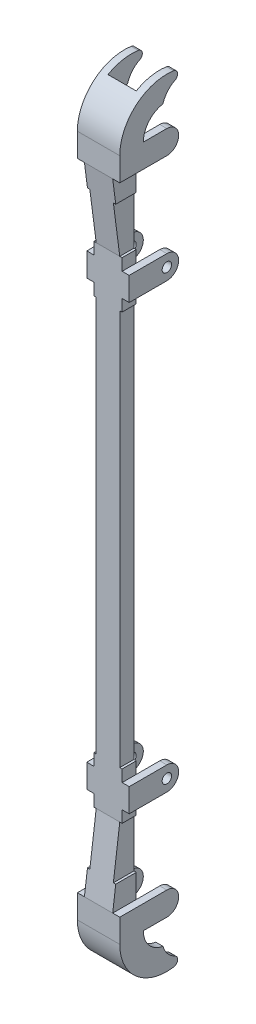
SolidWorks part; units mm, degrees
ref_plane "Ebene vorne" through (0, 0, 0) normal (0, 0, 1) x (1, 0, 0)
ref_plane "Ebene oben" through (0, 0, 0) normal (0, 1, 0) x (1, 0, 0)
ref_plane "Ebene rechts" through (0, 0, 0) normal (1, 0, 0) x (0, 0, -1)
sketch "Skizze2" plane through (0, 0, -2.5) normal (0, 0, 1) x (1, 0, 0)
  line L0 (2.5, -19.8333) -> (-2.5, -19.8333) construction
  line L1 (-2.5, -92.3333) -> (2.5, -92.3333)
  line L2 (-2.5, -92.3333) -> (-2.5, 52.6667)
  line L3 (-2.5, 52.6667) -> (2.5, 52.6667)
  line L4 (2.5, -92.3333) -> (2.5, 52.6667)
  line L5 (-2.5, -92.3333) -> (2.5, 52.6667) construction
  line L6 (-2.5, 52.6667) -> (2.5, -92.3333) construction
  line L7 (2.5, -3.25) -> (2.5, -36.4167) construction
  line L8 (2.5, 36.4167) -> (2.5, 3.25) construction
  line L9 (-2.5, 62.6667) -> (2.5, 62.6667) construction
  point P0 (0, -19.8333)
  dimension "D1" = 10
extrude "Aufsatz-Linear austragen1" add sketch "Skizze2" along normal blind 3 from surface at 2.5
sketch "Skizze3" plane through (2.5, 0, 0) normal (1, 0, 0) x (0, 0, -1)
  line L0 (0, 52.6667) -> (0, -92.3333) construction
  line L1 (0, 32.1667) -> (-3, 32.1667)
  line L2 (0, 32.1667) -> (0, 22.1667)
  line L3 (0, 22.1667) -> (-3, 22.1667)
  line L4 (-3, 32.1667) -> (-3, 22.1667)
  line L5 (-3, 52.6667) -> (-3, -92.3333) construction
  line L6 (-18.3634, 37.4167) -> (16.3978, 37.4167) construction
  line L7 (-3, 42.6667) -> (-3, 52.6667)
  line L8 (2.5, -19.8333) -> (-3, -19.8333) construction
  line L9 (2.5, -3.25) -> (2.5, -36.4167) construction
  line L10 (-3, -71.8333) -> (-3, -61.8333)
  line L11 (0, -61.8333) -> (-3, -61.8333)
  line L12 (0, -71.8333) -> (0, -61.8333)
  line L13 (0, -71.8333) -> (-3, -71.8333)
  line L14 (0, 52.6667) -> (-3, 52.6667)
  line L15 (0, 42.6667) -> (0, 52.6667)
  line L16 (0, 42.6667) -> (-3, 42.6667)
  line L17 (-3, 52.6667) -> (0, 52.6667) construction
  line L18 (0, -82.3333) -> (-3, -82.3333)
  line L19 (0, -82.3333) -> (0, -92.3333)
  line L20 (0, -92.3333) -> (-3, -92.3333)
  line L21 (-3, -82.3333) -> (-3, -92.3333)
  dimension "D1" = 10
  dimension "D2" = 42
extrude "Aufsatz-Linear austragen2" add sketch "Skizze3" along normal blind 0.5
sketch "Skizze4" plane through (3, 0, 0) normal (1, 0, 0) x (0, 0, -1)
  line L0 (-3, 24.6667) -> (-3, 29.6667)
  line L1 (-3, 29.6667) -> (5, 29.6667)
  line L2 (5, 24.6667) -> (-3, 24.6667)
  line L3 (5, 27.1667) -> (0, 27.1667) construction
  line L4 (-6.863, 38.6667) -> (7.9976, 38.6667) construction
  line L5 (5, 50.1667) -> (0, 50.1667) construction
  line L6 (2.5, -19.8333) -> (11.1884, -19.8333) construction
  line L7 (2.5, -3.25) -> (2.5, -36.4167) construction
  line L8 (5, -64.3333) -> (-3, -64.3333)
  line L9 (-3, -69.3333) -> (5, -69.3333)
  line L10 (-3, -64.3333) -> (-3, -69.3333)
  line L11 (-3, 32.1667) -> (-3, 22.1667) construction
  line L12 (0, 22.1667) -> (0, 32.1667) construction
  line L13 (5, 52.6667) -> (-3, 52.6667)
  line L14 (-3, 47.6667) -> (5, 47.6667)
  line L15 (-3, 52.6667) -> (-3, 47.6667)
  line L16 (5, -89.8333) -> (0, -89.8333) construction
  line L17 (-3, -92.3333) -> (-3, -87.3333)
  line L18 (-3, -87.3333) -> (5, -87.3333)
  line L19 (5, -92.3333) -> (-3, -92.3333)
  arc A0 (5, 29.6667) -> (5, 24.6667) centre (5, 27.1667) cw
  arc A1 (5, -69.3333) -> (5, -64.3333) centre (5, -66.8333) ccw
  arc A2 (5, 47.6667) -> (5, 52.6667) centre (5, 50.1667) ccw
  arc A3 (5, -87.3333) -> (5, -92.3333) centre (5, -89.8333) cw
  dimension "D1" = 5
  dimension "D2" = 8
extrude "Aufsatz-Linear austragen3" add sketch "Skizze4" along normal blind 1.5
ref_plane "Ebene1" through (0, 0, 0) normal (1, 0, 0) x (0, 0, -1)
mirror "Spiegeln1" about plane through (0, 0, 0) normal (1, 0, 0) of "Aufsatz-Linear austragen3", "Aufsatz-Linear austragen2"
sketch "Skizze5" plane through (4.5, 0, 0) normal (1, 0, 0) x (0, 0, -1)
  line L0 (13.8213, -19.8333) -> (7.5816, -19.8333) construction
  circle A0 centre (5, 27.1667) radius 1
  circle A1 centre (5, -66.8333) radius 1
  arc A2 (5, -69.3333) -> (5, -64.3333) centre (5, -66.8333) ccw construction
  dimension "D1" = 2
extrude "Schnitt-Linear austragen1" cut sketch "Skizze5" against normal through all
sketch "Skizze6" plane through (0, 0, 3) normal (0, 0, 1) x (1, 0, 0)
  line L0 (-4.5, 52.6667) -> (-4.5, 47.6667)
  line L1 (-4.5, 47.6667) -> (-3, 47.6667)
  line L2 (-3, 47.6667) -> (-3, 42.6667)
  line L3 (-3, 42.6667) -> (-2.5, 42.6667)
  line L4 (-2.5, 42.6667) -> (-2.5, 32.1667)
  line L5 (-2.5, 32.1667) -> (2.5, 32.1667)
  line L6 (2.5, 32.1667) -> (2.5, 42.6667)
  line L7 (2.5, 42.6667) -> (3, 42.6667)
  line L8 (3, 42.6667) -> (3, 47.6667)
  line L9 (3, 47.6667) -> (3, 42.6667) construction
  line L10 (3, 47.6667) -> (4.5, 47.6667)
  line L11 (4.5, 47.6667) -> (4.5, 52.6667)
  line L12 (4.5, 52.6667) -> (-4.5, 52.6667)
  line L13 (-25.0743, -19.8333) -> (29.9575, -19.8333) construction
  line L14 (4.5, -92.3333) -> (-4.5, -92.3333)
  line L15 (4.5, -87.3333) -> (4.5, -92.3333)
  line L16 (3, -87.3333) -> (4.5, -87.3333)
  line L17 (3, -82.3333) -> (3, -87.3333)
  line L18 (2.5, -82.3333) -> (3, -82.3333)
  line L19 (2.5, -71.8333) -> (2.5, -82.3333)
  line L20 (-2.5, -71.8333) -> (2.5, -71.8333)
  line L21 (-2.5, -82.3333) -> (-2.5, -71.8333)
  line L22 (-3, -82.3333) -> (-2.5, -82.3333)
  line L23 (-3, -87.3333) -> (-3, -82.3333)
  line L24 (-4.5, -87.3333) -> (-3, -87.3333)
  line L25 (-4.5, -92.3333) -> (-4.5, -87.3333)
  line L26 (4.5, -92.3333) -> (-4.5, -92.3333) construction
extrude "Aufsatz-Linear austragen4" add sketch "Skizze6" along normal blind 2
sketch "Skizze7" plane through (0, 0, 0) normal (1, 0, 0) x (0, 0, -1)
  line L0 (-3, 32.1667) -> (-5, 47.6667)
  line L1 (-3, 32.1667) -> (-3, 29.6667) construction
  line L2 (-5, 47.6667) -> (0, 47.6667) construction
  line L3 (-5, 47.6667) -> (-5, 32.1667)
  line L4 (-5, 32.1667) -> (-3, 32.1667)
  line L5 (-5, 42.6667) -> (-5, 47.6667) construction
  line L6 (-5, 32.1667) -> (-3, 32.1667) construction
  line L7 (-15.5336, -19.8333) -> (8.7319, -19.8333) construction
  line L8 (-5, -71.8333) -> (-3, -71.8333)
  line L9 (-5, -87.3333) -> (-5, -71.8333)
  line L10 (-3, -71.8333) -> (-5, -87.3333)
  line L11 (-5, -71.8333) -> (-3, -71.8333) construction
extrude "Schnitt-Linear austragen2" cut sketch "Skizze7" against normal through all and the other way through all
sketch "Skizze8" plane through (0, -92.3333, 0) normal (0, -1, 0) x (-1, 0, 0)
  line L1 (-2.5, -4.3548) -> (2.5, -4.3548)
  line L2 (-2.5, -4.3548) -> (-2.5, 0)
  line L3 (-2.5, 0) -> (2.5, 0)
  line L4 (2.5, -4.3548) -> (2.5, 0)
  point P5 (0, 0)
  point P6 (2.5, 0)
  point P8 (3, 0)
  point P10 (-2.5, -4.3548)
sketch "Skizze9" plane through (4.5, 0, 0) normal (1, 0, 0) x (0, 0, -1)
  line L0 (-5, -92.3333) -> (5, -92.3333) construction
  line L1 (-5, -92.3333) -> (-5, -87.3333) construction
  line L2 (0, -92.3333) -> (-5, -92.3333)
  line L3 (4.1627, -97.2627) -> (10.6747, -100.5673) construction
  line L4 (12.5, -102.3333) -> (182.5, -102.3333) construction
  arc A0 (-5, -92.3333) -> (10.6747, -100.5673) centre (5, -92.3333) ccw
  arc A1 (0, -92.3333) -> (4.1627, -97.2627) centre (5, -92.3333) ccw
  arc A3 (4.1627, -97.2627) -> (10.6747, -100.5673) centre (8.9645, -95.8689) ccw
  arc A4 (5.6317, -94.8) -> (12.2973, -96.9377) centre (8.9645, -95.8689) ccw construction
  point P12 (0, 0)
  point P17 (7.4633, -102.0252)
  dimension "D1" = 5
extrude "Aufsatz-Linear austragen6" add sketch "Skizze9" against normal up to surface (9 mm away)
sketch "Skizze10" plane through (0, -64.3333, 0) normal (0, 1, 0) x (1, 0, 0)
  line L0 (-4.5, 10.6747) -> (4.5, 10.6747) construction
  line L1 (-3, 10.6747) -> (3, 10.6747)
  line L2 (-3, 10.6747) -> (-3, 0)
  line L3 (-3, 0) -> (3, 0)
  line L4 (3, 10.6747) -> (3, 0)
  line L5 (-3, 5) -> (-3, 0) construction
  point P7 (-3, 0)
extrude "Schnitt-Linear austragen3" cut sketch "Skizze10" against normal through all and the other way through all
fillet "Verrundung1" radius 1 2 edges at (3.75, -100.5673, -10.6747) (-3.75, -100.5673, -10.6747)
ref_plane "Ebene2" through (0, -19.8333, 0) normal (0, -1, 0) x (-1, 0, 0)
mirror "Spiegeln2" about plane through (0, -19.8333, 0) normal (0, -1, 0) of "Verrundung1", "Schnitt-Linear austragen3", "Aufsatz-Linear austragen6"
